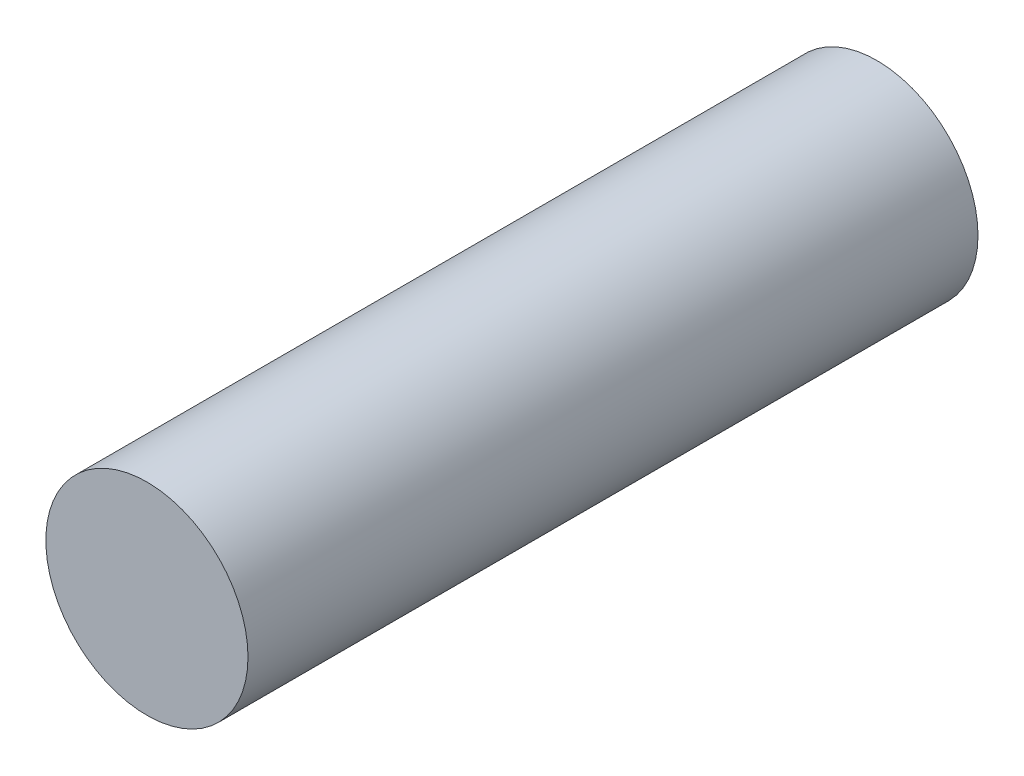
SolidWorks part; units mm, degrees
ref_plane "Front Plane" through (0, 0, 0) normal (0, 0, 1) x (1, 0, 0)
ref_plane "Top Plane" through (0, 0, 0) normal (0, 1, 0) x (1, 0, 0)
ref_plane "Right Plane" through (0, 0, 0) normal (1, 0, 0) x (0, 0, -1)
sketch "Sketch1" plane through (0, 0, 0) normal (0, 0, 1) x (1, 0, 0)
  circle A0 centre (0, 0) radius 9
  dimension "D1" = 18
extrude "Boss-Extrude1" add sketch "Sketch1" along normal blind 65
